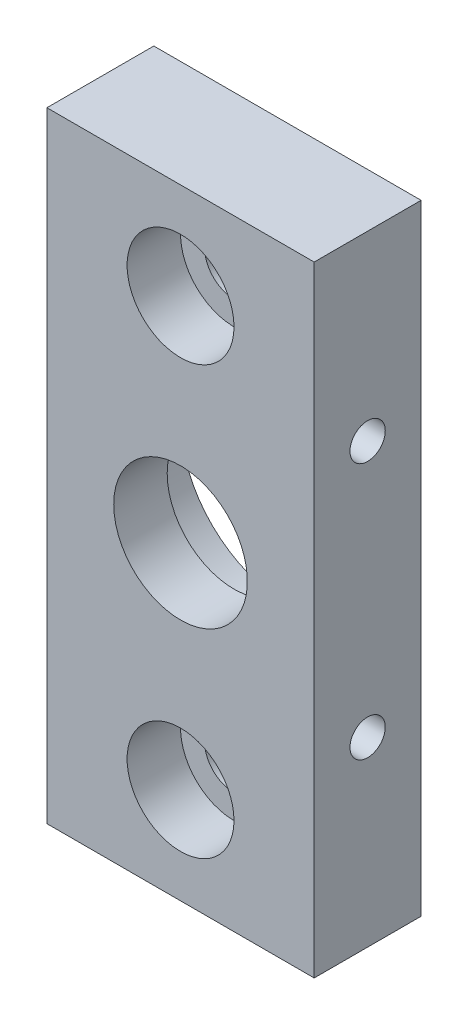
SolidWorks part; units mm, degrees
material "3.1325 (EN-AW 2017A)"
ref_plane "Plan de face" through (0, 0, 0) normal (0, 0, 1) x (1, 0, 0)
ref_plane "Plan de dessus" through (0, 0, 0) normal (0, 1, 0) x (1, 0, 0)
ref_plane "Plan de droite" through (0, 0, 0) normal (1, 0, 0) x (0, 0, -1)
sketch "Esquisse1" plane through (0, 0, 0) normal (0, 0, 1) x (1, 0, 0)
  line L1 (-12.5, -29) -> (12.5, -29)
  line L2 (-12.5, -29) -> (-12.5, 29)
  line L3 (-12.5, 29) -> (12.5, 29)
  line L4 (12.5, -29) -> (12.5, 29)
  line L5 (-12.5, -29) -> (12.5, 29) construction
  line L6 (-12.5, 29) -> (12.5, -29) construction
  point P0 (0, 0)
  dimension "D1" = 25
  dimension "D2" = 58
extrude "Boss.-Extru.1" add sketch "Esquisse1" along normal blind 10
sketch "Esquisse3" plane through (0, 0, 0) normal (0, 0, -1) x (-1, 0, 0)
  circle A0 centre (0, 0) radius 10
extrude "Enlèv. mat.-Extru.2" cut sketch "Esquisse3" against normal blind 5
sketch "Esquisse4" plane through (0, 0, 5) normal (0, 0, -1) x (-1, 0, 0)
  circle A0 centre (0, 0) radius 6.25
extrude "Enlèv. mat.-Extru.3" cut sketch "Esquisse4" against normal through all
hole_wizard "Chambrage pour vis à tête hexagonale M51" positions "Esquisse6" profile "Esquisse5" counterbore size "M5" standard "ISO" end condition through all
sketch "Esquisse6" plane through (0, 0, 10) normal (0, 0, 1) x (1, 0, 0)
  line L0 (12.5, -29) -> (12.5, 29) construction
  point P0 (0, -20)
  dimension "D1" = 12.5
  dimension "D2" = 20
sketch "Esquisse5" plane through (0, -20, 10) normal (1, 0, 0) x (0, -1, 0)
  line L0 (0, 0) -> (0, 10)
  line L1 (0, 10) -> (2.75, 10)
  line L3 (2.75, 10) -> (2.75, 5)
  line L4 (2.75, 5) -> (5, 5)
  line L5 (5, 5) -> (5, 0)
  line L7 (5, 0) -> (0, 0)
  line L11 (0, -6.35) -> (0, 107.95) construction
  dimension "Diamètre du perçage jusqu'au prochain" = 5.5
  dimension "Profondeur du perçage jusqu'au prochain" = 10
  dimension "Diamètre du chambrage" = 10
  dimension "Profondeur du chambrage" = 5
hole_wizard "Chambrage pour vis à tête hexagonale M53" positions "Esquisse10" profile "Esquisse9" counterbore size "M5" standard "ISO" end condition through all
sketch "Esquisse10" plane through (0, 0, 10) normal (0, 0, 1) x (1, 0, 0)
  line L0 (12.5, -29) -> (12.5, 29) construction
  point P0 (0, 20)
  dimension "D1" = 12.5
  dimension "D2" = 20
sketch "Esquisse9" plane through (0, 20, 10) normal (1, 0, 0) x (0, -1, 0)
  line L0 (0, 0) -> (0, 10)
  line L1 (0, 10) -> (2.75, 10)
  line L3 (2.75, 10) -> (2.75, 5)
  line L4 (2.75, 5) -> (5, 5)
  line L5 (5, 5) -> (5, 0)
  line L7 (5, 0) -> (0, 0)
  line L11 (0, -6.35) -> (0, 107.95) construction
  dimension "Diamètre du perçage jusqu'au prochain" = 5.5
  dimension "Profondeur du perçage jusqu'au prochain" = 10
  dimension "Diamètre du chambrage" = 10
  dimension "Profondeur du chambrage" = 5
hole_wizard "Trou taraudé M43" positions "Esquisse12" profile "Esquisse11" tap size "M4" standard "ISO" end condition through all
sketch "Esquisse12" plane through (12.5, 0, 0) normal (1, 0, 0) x (0, 0, -1)
  line L2 (0, -29) -> (0, 29) construction
  point P0 (-5, 12)
  point P11 (0, 0)
  dimension "D1" = 12
cosmetic thread "Filetage de perçage2" parameters "D2"=4
sketch "Esquisse11" plane through (12.5, 12, 5) normal (0, 1, 0) x (0, 0, -1)
  line L0 (0, 0) -> (0, 25)
  line L1 (0, 25) -> (1.65, 25)
  line L2 (1.65, 25) -> (1.65, 0)
  line L5 (1.65, 0) -> (0, 0)
  line L11 (0, -6.35) -> (0, 107.95) construction
  dimension "Diamètre du trou pour taraudage jusqu'au prochain" = 3.3
  dimension "Profondeur du trou pour taraudage jusqu'au prochain" = 25
hole_wizard "Trou taraudé M42" positions "Esquisse14" profile "Esquisse13" tap size "M4" standard "ISO" end condition through all
sketch "Esquisse14" plane through (-12.5, 0, 0) normal (-1, 0, 0) x (0, 0, 1)
  line L2 (0, 29) -> (0, -29) construction
  point P0 (5, -12)
  point P11 (0, 0)
  dimension "D1" = 12
sketch "Esquisse13" plane through (-12.5, -12, 5) normal (0, 1, 0) x (0, 0, 1)
  line L0 (0, 0) -> (0, 25)
  line L1 (0, 25) -> (1.65, 25)
  line L2 (1.65, 25) -> (1.65, 0)
  line L5 (1.65, 0) -> (0, 0)
  line L11 (0, -6.35) -> (0, 107.95) construction
  dimension "Diamètre du trou pour taraudage jusqu'au prochain" = 3.3
  dimension "Profondeur du trou pour taraudage jusqu'au prochain" = 25
cosmetic thread "Filetage de perçage1" parameters "D2"=4
